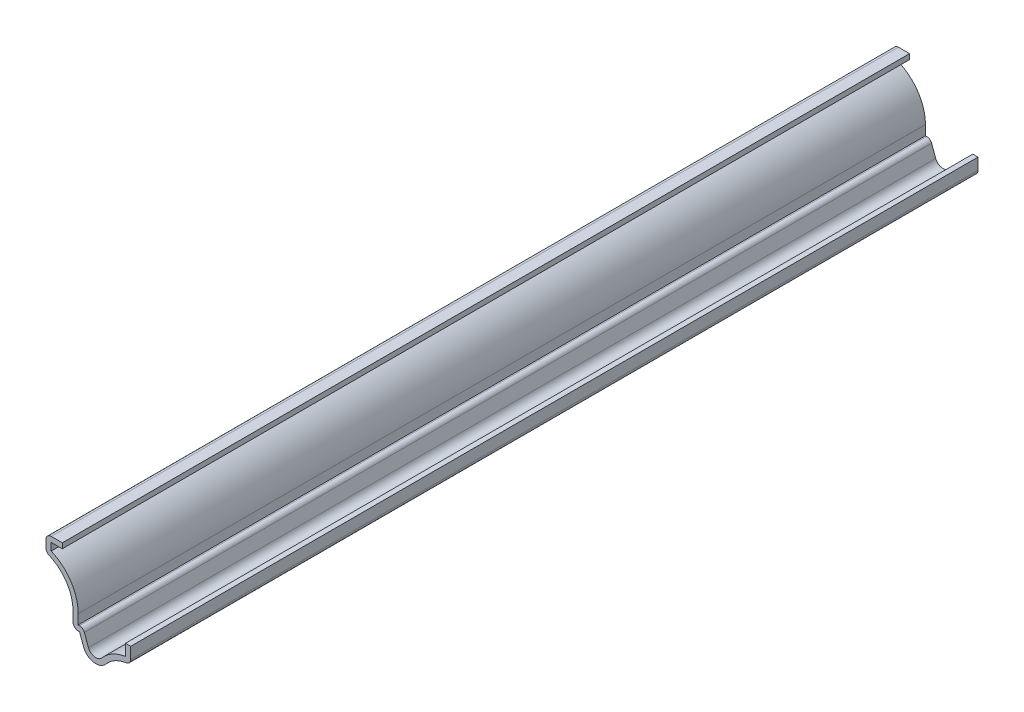
SolidWorks part; units mm, degrees
ref_plane "Front Plane" through (0, 0, 0) normal (0, 0, 1) x (1, 0, 0)
ref_plane "Top Plane" through (0, 0, 0) normal (0, 1, 0) x (1, 0, 0)
ref_plane "Right Plane" through (0, 0, 0) normal (1, 0, 0) x (0, 0, -1)
sketch "Sketch1" plane through (0, 0, 0) normal (0, 0, 1) x (1, 0, 0)
  line L0 (0, 7.9375) -> (0, 3.9688)
  line L1 (0, 0) -> (-25.5227, 0) construction
  line L2 (-11.4912, 2.0771) -> (-12.4808, 4.7625)
  line L3 (-12.4808, 4.7625) -> (-14.0683, 4.7625)
  line L4 (-14.0683, 4.7625) -> (-14.0683, 8.4077)
  line L5 (-20.6375, 17.4625) -> (-20.6375, 21.4312)
  line L6 (-20.6375, 21.4312) -> (-16.6687, 21.4312)
  arc A0 (0, 3.9688) -> (-6.08, 1.1339) centre (0, -3.9688) ccw
  arc A1 (-6.08, 1.1339) -> (-11.4912, 2.0771) centre (-8.512, 3.175) cw
  arc A2 (-14.0683, 8.4077) -> (-20.6375, 17.4625) centre (-23.5933, 8.4077) ccw
  point P14 (0, 0)
extrude "Extrude-Thin1" add sketch "Sketch1" against normal blind 206.375 thin
fillet "Fillet1" radius 1.27 5 edges at (0, 3.9688, -103.1875) (-14.0683, 4.7625, -103.1875) (-11.5953, 6.0325, -103.1875) (-20.6375, 17.4625, -103.1875) (-20.6375, 21.4312, -103.1875)
equation "\"D1@Extrude-Thin1\"=\"D12@Sketch1\"*10"
